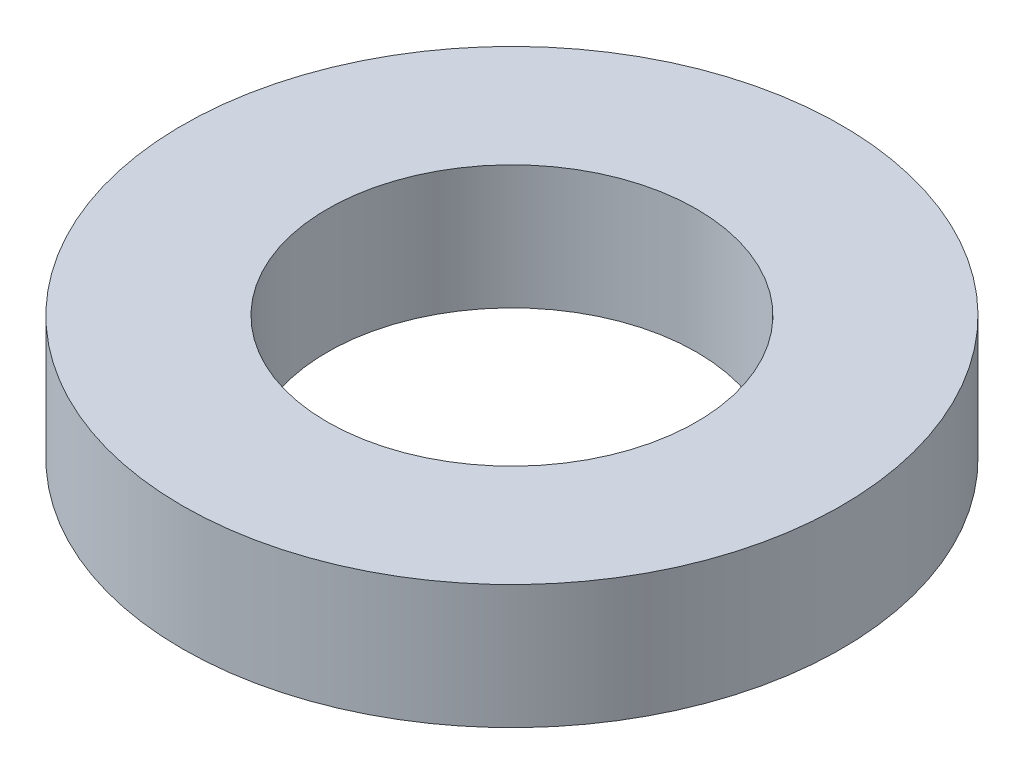
SolidWorks part; units mm, degrees
ref_plane "Front" through (0, 0, 0) normal (0, 0, 1) x (1, 0, 0)
ref_plane "Top" through (0, 0, 0) normal (0, 1, 0) x (1, 0, 0)
ref_plane "Right" through (0, 0, 0) normal (1, 0, 0) x (0, 0, -1)
sketch "Sketch1" plane through (0, 0, 0) normal (0, 1, 0) x (1, 0, 0)
  circle A0 centre (0, 0) radius 3.175
  dimension "D1" = 6.35
extrude "Extrude1" add sketch "Sketch1" along normal blind 1.1938
sketch "Sketch2" plane through (0, 1.1938, 0) normal (0, 1, 0) x (-1, 0, 0)
  circle A0 centre (0, 0) radius 1.778
  dimension "D1" = 3.556
extrude "Cut-Extrude1" cut sketch "Sketch2" against normal blind 1.1938
